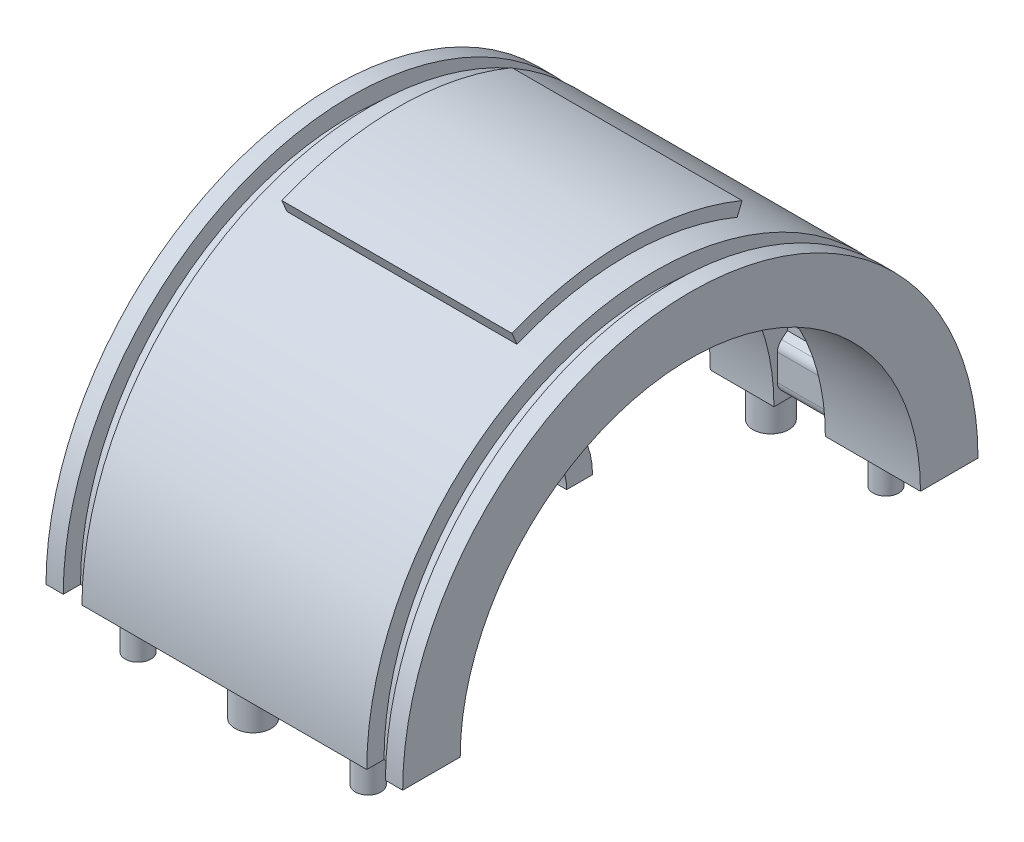
SolidWorks part; units mm, degrees
ref_plane "Front Plane" through (0, 0, 0) normal (0, 0, 1) x (1, 0, 0)
ref_plane "Top Plane" through (0, 0, 0) normal (0, 1, 0) x (1, 0, 0)
ref_plane "Right Plane" through (0, 0, 0) normal (1, 0, 0) x (0, 0, -1)
sketch "Sketch1" plane through (0, 0, 0) normal (0, 1, 0) x (1, 0, 0)
  line L0 (0, 0) -> (155.1991, 0) construction
  line L1 (155.1991, 0) -> (-158.5278, 0) construction
  line L2 (0, 0) -> (0, -90.4212) construction
  line L3 (0, 0) -> (0, 195.4795) construction
  line L9 (24.75, 47) -> (28, 47)
  line L10 (31, 50) -> (28, 50)
  line L15 (31, 50) -> (31, 40)
  line L16 (31, 40) -> (-26, 40)
  line L22 (-31, 50) -> (-31, 40)
  line L23 (31, 50) -> (28, 49.5161) construction
  line L24 (31, 40) -> (-24.75, 48.9919) construction
  line L26 (-24.75, 50) -> (-24.75, 47)
  line L27 (-24.75, 47) -> (-28, 47)
  line L28 (-28, 50) -> (-28, 47)
  line L29 (24.75, 50) -> (-24.75, 50)
  line L30 (24.75, 48.9919) -> (-26, 40.8065) construction
  line L35 (28, 50) -> (28, 47)
  line L36 (24.75, 50) -> (24.75, 47)
  line L38 (-28, 50) -> (-31, 50)
  line L39 (-28, 49.5161) -> (-31, 50) construction
  line L40 (-26, 77.8545) -> (-26, 16.5) construction
  line L41 (-35, 76.0219) -> (-35, -31.7141) construction
  line L42 (-31, 40) -> (-31, -27.11) construction
  line L43 (-97.0302, 16.5) -> (67.6651, 16.5) construction
  line L44 (-97.0302, 14) -> (77.1364, 14) construction
  line L45 (-85.0595, 9.5) -> (85.95, 9.5) construction
  line L46 (-80.3239, 27.25) -> (68.7175, 27.25) construction
  line L47 (-10, 63.6566) -> (-10, -23.2952) construction
  line L48 (-28, 68.9882) -> (-28, -37.4297) construction
  line L49 (-24.75, 67.96) -> (-24.75, -40.5143) construction
  line L50 (-18.153, 23.85) -> (-54.2967, 23.85) construction
  line L51 (-18.153, 18.7) -> (-49.456, 18.7) construction
  line L52 (-9.9469, 14) -> (-10, 9.5)
  spline S0 degree 3 poles (-31, 40) (-32.9396, 37.5406) (-36.9339, 27.5823) (-30.0824, 11.7757) (-17.9219, 9.5) (-10, 9.5) knots 0 0 0 0 0.268185 0.444495 0.82256 0.82256 0.82256 0.82256
  spline S1 degree 3 poles (-26, 40) (-27.0137, 36.8092) (-29.3451, 27.8281) (-24.5235, 15.3947) (-15.5263, 14.8685) (-9.9469, 14) knots 0 0 0 0 0.285239 0.456571 0.779818 0.779818 0.779818 0.779818
  point P3 (0, 45)
  point P11 (-26.375, 50)
  dimension "D14" = 3
  dimension "D1" = 62
  dimension "D2" = 10
  dimension "D3" = 50
  dimension "D4" = 3
  dimension "D5" = 3
  dimension "D6" = 5
  dimension "D7" = 4
  dimension "D8" = 23.5
  dimension "D9" = 26
  dimension "D10" = 30.5
  dimension "D11" = 12.75
  dimension "D12" = 21
  dimension "D13" = 10
  dimension "D15" = 6.25
  dimension "D16" = 16.15
  dimension "D17" = 21.3
revolve "Revolve1" add sketch "Sketch1" angle 180 about L0
ref_plane "Plane1" through (0, 0, 0) normal (0, -1, 0) x (-1, 0, 0)
sketch "Sketch2" plane through (0, 0, 0) normal (0, -1, 0) x (-1, 0, 0)
  line L0 (0, -50) -> (0, 61.0168) construction
  line L1 (-24.75, -50) -> (24.75, -50) construction
  line L2 (-31, -45) -> (31, -45) construction
  line L3 (-31, -40) -> (-31, -50) construction
  line L4 (31, -50) -> (31, -40) construction
  line L5 (0, 0) -> (-87.0535, 0) construction
  line L6 (-87.0535, 0) -> (84.579, 0) construction
sketch "Sketch5" plane through (0, 0, 0) normal (0, -1, 0) x (-1, 0, 0)
  line L0 (0, 27.5) -> (0, -27.5) construction
  line L5 (-31, -40) -> (-50031, -40) construction
  line L6 (40.2344, 0) -> (-50.8563, 0) construction
  line L7 (-27.5, 0) -> (27.5, 0) construction
  line L16 (-31, -50) -> (-50031, -50) construction
  line L17 (-20, -25.5251) -> (-20, -50025.5251) construction
  line L19 (20, -24.2663) -> (20, -50024.2663) construction
  line L20 (31, -45) -> (-31, -45) construction
  line L21 (0, -50) -> (0, 61.0168) construction
  circle A0 centre (0, -45) radius 3.1275
  circle A1 centre (-20, -45) radius 2.2275
  circle A2 centre (20, -45) radius 2.2275
  dimension "D3" = 6.255
  dimension "D4" = 4.455
  dimension "D1" = 20
  dimension "D2" = 20
sketch "Sketch6" plane through (0, 0, 0) normal (1, 0, 0) x (0, 0, -1)
  line L0 (-14, 0) -> (-9.5, 0)
  line L2 (9.5, 0) -> (14, 0)
  arc A0 (9.5, 0) -> (-9.5, 0) centre (0, 0) ccw
  arc A1 (14, 0) -> (-14, 0) centre (0, 0) ccw
extrude "Boss-Extrude1" add sketch "Sketch6" against normal up to surface (31 mm away) up to face at (-31, 22.5, 0)
ref_plane "Plane3" through (31, 0, 0) normal (1, 0, 0) x (0, 0, -1)
sketch "Sketch7" plane through (31, 0, 0) normal (1, 0, 0) x (0, 0, -1)
  line L0 (4.7883, 13.1557) -> (13.6808, 37.5877)
  line L1 (-4.7883, 13.1557) -> (-13.6808, 37.5877)
  line L2 (0, 27.5) -> (0, -27.5) construction
  arc A0 (13.6808, 37.5877) -> (-13.6808, 37.5877) centre (0, 0) ccw
  arc A1 (4.7883, 13.1557) -> (-4.7883, 13.1557) centre (0, 0) ccw
  dimension "D1" = 20
  dimension "D2" = 20
extrude "Cut-Extrude1" cut sketch "Sketch7" against normal blind 100
pattern_circular "CirPattern1" count 6 over 360 about axis through (0, 0, 0) along (1, 0, 0) of "Cut-Extrude1"
extrude "Boss-Extrude2" add sketch "Sketch5" along normal blind 7.155
mirror "Mirror1" about plane through (0, 0, 0) normal (0, 0, 1) of "Boss-Extrude2"
ref_plane "Plane4" through (10, 0, 0) normal (1, 0, 0) x (0, 0, -1)
sketch "Sketch8" plane through (10, 0, 0) normal (1, 0, 0) x (0, 0, -1)
  line L0 (66.452, 0) -> (50066.452, 0) construction
  line L2 (50, 0) -> (50, 50000) construction
  line L3 (40.6105, 8.855) -> (42.331, 10.2987)
  line L4 (40, 0) -> (40, 50000) construction
  line L5 (40.6105, 8.855) -> (40.6105, 16.2274) construction
  line L6 (0, 31.9) -> (0, -31.9) construction
  line L7 (40, 0) -> (40.6105, 0)
  line L8 (40.6105, 0) -> (40.6105, 8.855)
  line L13 (42.331, 10.2987) -> (42.331, 13.6842)
  line L14 (40.6105, 15.3164) -> (45.9076, 15.3164) construction
  line L15 (45.9076, 15.3164) -> (30.0457, 15.3164) construction
  line L17 (35.5222, 18.3895) -> (35.5222, 0)
  line L18 (35.5222, 0) -> (40, 0)
  line L19 (34.2362, 8.855) -> (46.5106, 8.855) construction
  line L20 (40, 15.3164) -> (42.331, 13.6842)
  line L21 (35.5222, 18.3895) -> (40, 15.3164)
  arc A0 (40, 0) -> (-40, 0) centre (0, 0) ccw
  dimension "D1" = 40
  dimension "D2" = 50
  dimension "D3" = 0.6105
  dimension "D4" = 8.855
  dimension "D5" = 1.7205
  dimension "D6" = 3.3855
  dimension "D7" = 40
  dimension "D8" = 35
extrude "Cut-Extrude2" cut sketch "Sketch8" against normal mid plane 8.9355 contours L7 L8 L3 L13 L20 L21 L17 L18
mirror "Mirror2" about plane through (0, 0, 0) normal (1, 0, 0) of "Cut-Extrude2"
mirror "Mirror3" about plane through (0, 0, 0) normal (0, 0, 1) of "Cut-Extrude2", "Mirror2"
chamfer "Chamfer1" distance 2.5 angle 45 4 edges at (10, 0, -40.6105) (-10, 0, -40.6105) (-10, 0, 40.6105) (10, 0, 40.6105)
fillet "Fillet1" radius 2 4 edges at (-10, 2.5, -40.6105) (10, 2.5, -40.6105) (-10, 2.5, 40.6105) (10, 2.5, 40.6105)
fillet "Fillet2" radius 2 4 edges at (-10, 8.855, 40.6105) (10, 8.855, 40.6105) (-10, 8.855, -40.6105) (10, 8.855, -40.6105)
sketch "Sketch9" plane through (0, 0, 0) normal (0, 0, 1) x (1, 0, 0)
  line L0 (31, 49.9034) -> (31, -49950.0966) construction
  line L2 (-31, 50) -> (-31, -49950) construction
  line L4 (0, 1050) -> (0, 47.7491) construction
  line L5 (24.75, 50) -> (-24.75, 50) construction
  line L7 (20, 50) -> (-20, 50)
  line L8 (-20, 52.2509) -> (20, 52.2509)
  line L9 (-20, 52.2509) -> (-20, 50)
  line L11 (20, 52.2509) -> (20, 50)
  line L12 (-20, 52.2509) -> (0, 50) construction
  line L13 (0, 50) -> (20, 52.2509) construction
  line L14 (43.5267, 0) -> (-58.6572, 0) construction
  line L15 (0, 0) -> (87.0535, 0) construction
  line L16 (87.0535, 0) -> (-84.579, 0) construction
  point P9 (0, 50)
  point P10 (0, 50)
  dimension "D1" = 62
  dimension "D2" = 40
  dimension "D3" = 20
revolve "Revolve2" add sketch "Sketch9" angle 45 mid plane about L14
